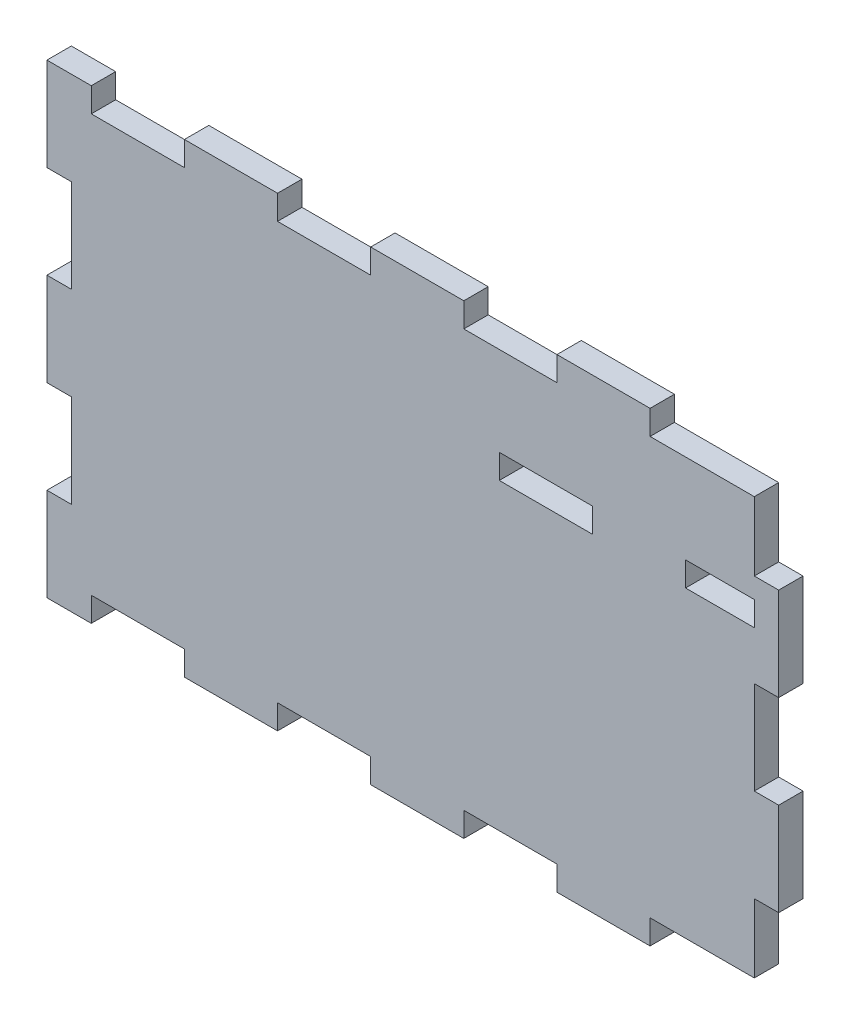
SolidWorks part; units mm, degrees
ref_plane "Alzado" through (0, 0, 0) normal (0, 0, 1) x (1, 0, 0)
ref_plane "Planta" through (0, 0, 0) normal (0, 1, 0) x (1, 0, 0)
ref_plane "Vista lateral" through (0, 0, 0) normal (1, 0, 0) x (0, 0, -1)
sketch "Croquis2" plane through (0, 0, 0) normal (0, 0, 1) x (1, 0, 0)
  line L11 (-60.2904, -48.8443) -> (-52.7904, -48.8443)
  line L12 (-52.7904, -48.8443) -> (-52.7904, -45.8443)
  line L13 (-52.7904, -45.8443) -> (-31.7904, -45.8443)
  line L14 (-31.7904, -45.8443) -> (-31.7904, -48.8443)
  line L15 (-31.7904, -48.8443) -> (-10.7904, -48.8443)
  line L16 (-10.7904, -48.8443) -> (-10.7904, -45.8443)
  line L17 (-10.7904, -45.8443) -> (10.2096, -45.8443)
  line L18 (10.2096, -45.8443) -> (10.2096, -48.8443)
  line L19 (10.2096, -48.8443) -> (31.2096, -48.8443)
  line L20 (31.2096, -48.8443) -> (31.2096, -45.8443)
  line L21 (31.2096, -45.8443) -> (52.2096, -45.8443)
  line L22 (52.2096, -45.8443) -> (52.2096, -48.8443)
  line L23 (52.2096, -48.8443) -> (73.2096, -48.8443)
  line L24 (73.2096, -48.8443) -> (73.2096, -45.8443)
  line L25 (73.2096, -45.8443) -> (94.2096, -45.8443)
  line L26 (94.2096, -45.8443) -> (96.7096, -45.8443)
  line L27 (96.7096, -45.8443) -> (96.7096, -30.3443)
  line L28 (96.7096, -30.3443) -> (99.7096, -30.3443)
  line L29 (99.7096, -30.3443) -> (99.7096, -9.3443)
  line L30 (99.7096, -9.3443) -> (96.7096, -9.3443)
  line L31 (96.7096, -9.3443) -> (96.7096, 11.6557)
  line L32 (96.7096, 11.6557) -> (99.7096, 11.6557)
  line L33 (99.7096, 11.6557) -> (99.7096, 32.6557)
  line L34 (99.7096, 32.6557) -> (96.7096, 32.6557)
  line L35 (96.7096, 32.6557) -> (96.7096, 48.1557)
  line L36 (96.7096, 48.1557) -> (73.2096, 48.1557)
  line L37 (73.2096, 48.1557) -> (73.2096, 51.1557)
  line L38 (73.2096, 51.1557) -> (52.2096, 51.1557)
  line L39 (52.2096, 51.1557) -> (52.2096, 48.1557)
  line L40 (52.2096, 48.1557) -> (31.2096, 48.1557)
  line L41 (31.2096, 48.1557) -> (31.2096, 51.1557)
  line L42 (31.2096, 51.1557) -> (10.2096, 51.1557)
  line L43 (10.2096, 51.1557) -> (10.2096, 48.1557)
  line L44 (10.2096, 48.1557) -> (-10.7904, 48.1557)
  line L45 (-10.7904, 48.1557) -> (-10.7904, 51.1557)
  line L46 (-10.7904, 51.1557) -> (-31.7904, 51.1557)
  line L47 (-31.7904, 51.1557) -> (-31.7904, 48.1557)
  line L48 (-31.7904, 48.1557) -> (-52.7904, 48.1557)
  line L49 (-52.7904, 48.1557) -> (-52.7904, 51.1557)
  line L50 (-52.7904, 51.1557) -> (-60.2904, 51.1557)
  line L54 (96.7096, 1.1557) -> (-60.2904, 1.1557) construction
  line L55 (-60.2904, 32.6557) -> (-57.2904, 32.6557)
  line L56 (60.2096, 28.0657) -> (39.2096, 28.0657)
  line L57 (96.7096, 28.0657) -> (81.2096, 28.0657)
  line L58 (96.7096, 28.0657) -> (96.7096, 22.5657)
  line L59 (96.7096, 22.5657) -> (81.2096, 22.5657)
  line L60 (81.2096, 28.0657) -> (81.2096, 22.5657)
  line L61 (60.2096, 28.0657) -> (60.2096, 22.5657)
  line L62 (60.2096, 22.5657) -> (39.2096, 22.5657)
  line L63 (39.2096, 28.0657) -> (39.2096, 22.5657)
  line L68 (-60.2904, -48.8443) -> (-60.2904, -30.3443)
  line L69 (-60.2904, 11.6557) -> (-57.2904, 11.6557)
  line L70 (-57.2904, 32.6557) -> (-57.2904, 11.6557)
  line L71 (-60.2904, 32.6557) -> (-60.2904, 51.1557)
  line L72 (-57.2904, -30.3443) -> (-57.2904, -9.3443)
  line L73 (-60.2904, -9.3443) -> (-57.2904, -9.3443)
  line L74 (-60.2904, -30.3443) -> (-57.2904, -30.3443)
  line L75 (-60.2904, -9.3443) -> (-60.2904, 11.6557)
  point P4 (-58.7904, 32.6557)
  point P11 (99.7096, 22.1557)
  dimension "D1" = 100
  dimension "D2" = 160
  dimension "D3" = 15.5
  dimension "D4" = 5.5
  dimension "D5" = 0
  dimension "D6" = 23.09
  dimension "D7" = 21
  dimension "D8" = 5.5
  dimension "D9" = 21
  dimension "D10" = 21
  dimension "D11" = 18.5
  dimension "D12" = 21
  dimension "D13" = 21
  dimension "D14" = 18.5
  dimension "D15" = 3
extrude "Saliente-Extruir1" add sketch "Croquis2" along normal blind 5.5
sketch "Croquis3" plane through (0, 51.1557, 0) normal (0, 1, 0) x (1, 0, 0)
  line L0 (73.2096, 0) -> (52.2096, 0) construction
  line L1 (52.2096, 0) -> (52.2096, -5.5) construction
  line L2 (52.2096, -5.5) -> (73.2096, -5.5) construction
  line L3 (73.2096, -5.5) -> (73.2096, 0) construction
  line L4 (31.2096, 0) -> (10.2096, 0) construction
  line L5 (10.2096, 0) -> (10.2096, -5.5) construction
  line L6 (10.2096, -5.5) -> (31.2096, -5.5) construction
  line L7 (31.2096, -5.5) -> (31.2096, 0) construction
  line L8 (-10.7904, 0) -> (-31.7904, 0) construction
  line L9 (-31.7904, 0) -> (-31.7904, -5.5) construction
  line L10 (-31.7904, -5.5) -> (-10.7904, -5.5) construction
  line L11 (-10.7904, -5.5) -> (-10.7904, 0) construction
  line L12 (-52.7904, 0) -> (-60.2904, 0) construction
  line L13 (-60.2904, 0) -> (-60.2904, -5.5) construction
  line L14 (-60.2904, -5.5) -> (-52.7904, -5.5) construction
  line L15 (-52.7904, -5.5) -> (-52.7904, 0) construction
  line L16 (73.2096, 0) -> (52.2096, 0)
  line L17 (52.2096, 0) -> (52.2096, -5.5)
  line L18 (52.2096, -5.5) -> (73.2096, -5.5)
  line L19 (73.2096, -5.5) -> (73.2096, 0)
  line L20 (31.2096, 0) -> (10.2096, 0)
  line L21 (10.2096, 0) -> (10.2096, -5.5)
  line L22 (10.2096, -5.5) -> (31.2096, -5.5)
  line L23 (31.2096, -5.5) -> (31.2096, 0)
  line L24 (-10.7904, 0) -> (-31.7904, 0)
  line L25 (-31.7904, 0) -> (-31.7904, -5.5)
  line L26 (-31.7904, -5.5) -> (-10.7904, -5.5)
  line L27 (-10.7904, -5.5) -> (-10.7904, 0)
  line L28 (-52.7904, 0) -> (-60.2904, 0)
  line L29 (-60.2904, 0) -> (-60.2904, -5.5)
  line L30 (-60.2904, -5.5) -> (-52.7904, -5.5)
  line L31 (-52.7904, -5.5) -> (-52.7904, 0)
extrude "Saliente-Extruir2" add sketch "Croquis3" along normal blind 2.5
sketch "Croquis4" plane through (-60.2904, 0, 0) normal (-1, 0, 0) x (0, 0, 1)
  line L0 (0, -30.3443) -> (0, -48.8443) construction
  line L1 (0, -48.8443) -> (5.5, -48.8443) construction
  line L2 (5.5, -48.8443) -> (5.5, -30.3443) construction
  line L3 (5.5, -30.3443) -> (0, -30.3443) construction
  line L4 (0, 11.6557) -> (0, -9.3443) construction
  line L5 (0, -9.3443) -> (5.5, -9.3443) construction
  line L6 (5.5, -9.3443) -> (5.5, 11.6557) construction
  line L7 (5.5, 11.6557) -> (0, 11.6557) construction
  line L8 (0, 53.6557) -> (0, 32.6557) construction
  line L9 (0, 32.6557) -> (5.5, 32.6557) construction
  line L10 (5.5, 32.6557) -> (5.5, 53.6557) construction
  line L11 (5.5, 53.6557) -> (0, 53.6557) construction
  line L12 (0, -30.3443) -> (0, -48.8443)
  line L13 (0, -48.8443) -> (5.5, -48.8443)
  line L14 (5.5, -48.8443) -> (5.5, -30.3443)
  line L15 (5.5, -30.3443) -> (0, -30.3443)
  line L16 (0, 11.6557) -> (0, -9.3443)
  line L17 (0, -9.3443) -> (5.5, -9.3443)
  line L18 (5.5, -9.3443) -> (5.5, 11.6557)
  line L19 (5.5, 11.6557) -> (0, 11.6557)
  line L20 (0, 53.6557) -> (0, 32.6557)
  line L21 (0, 32.6557) -> (5.5, 32.6557)
  line L22 (5.5, 32.6557) -> (5.5, 53.6557)
  line L23 (5.5, 53.6557) -> (0, 53.6557)
extrude "Saliente-Extruir3" add sketch "Croquis4" along normal blind 2.5
sketch "Croquis5" plane through (0, -48.8443, 0) normal (0, -1, 0) x (1, 0, 0)
  line L0 (-62.7904, 0) -> (-52.7904, 0) construction
  line L1 (-52.7904, 0) -> (-52.7904, 5.5) construction
  line L2 (-52.7904, 5.5) -> (-62.7904, 5.5) construction
  line L3 (-62.7904, 5.5) -> (-62.7904, 0) construction
  line L4 (-31.7904, 0) -> (-10.7904, 0) construction
  line L5 (-10.7904, 0) -> (-10.7904, 5.5) construction
  line L6 (-10.7904, 5.5) -> (-31.7904, 5.5) construction
  line L7 (-31.7904, 5.5) -> (-31.7904, 0) construction
  line L8 (10.2096, 0) -> (31.2096, 0) construction
  line L9 (31.2096, 0) -> (31.2096, 5.5) construction
  line L10 (31.2096, 5.5) -> (10.2096, 5.5) construction
  line L11 (10.2096, 5.5) -> (10.2096, 0) construction
  line L12 (52.2096, 0) -> (73.2096, 0) construction
  line L13 (73.2096, 0) -> (73.2096, 5.5) construction
  line L14 (73.2096, 5.5) -> (52.2096, 5.5) construction
  line L15 (52.2096, 5.5) -> (52.2096, 0) construction
  line L16 (-62.7904, 0) -> (-52.7904, 0)
  line L17 (-52.7904, 0) -> (-52.7904, 5.5)
  line L18 (-52.7904, 5.5) -> (-62.7904, 5.5)
  line L19 (-62.7904, 5.5) -> (-62.7904, 0)
  line L20 (-31.7904, 0) -> (-10.7904, 0)
  line L21 (-10.7904, 0) -> (-10.7904, 5.5)
  line L22 (-10.7904, 5.5) -> (-31.7904, 5.5)
  line L23 (-31.7904, 5.5) -> (-31.7904, 0)
  line L24 (10.2096, 0) -> (31.2096, 0)
  line L25 (31.2096, 0) -> (31.2096, 5.5)
  line L26 (31.2096, 5.5) -> (10.2096, 5.5)
  line L27 (10.2096, 5.5) -> (10.2096, 0)
  line L28 (52.2096, 0) -> (73.2096, 0)
  line L29 (73.2096, 0) -> (73.2096, 5.5)
  line L30 (73.2096, 5.5) -> (52.2096, 5.5)
  line L31 (52.2096, 5.5) -> (52.2096, 0)
extrude "Saliente-Extruir4" add sketch "Croquis5" along normal blind 2.5
sketch "Croquis6" plane through (99.7096, 0, 0) normal (1, 0, 0) x (0, 0, -1)
  line L0 (0, 11.6557) -> (0, 32.6557) construction
  line L1 (0, 32.6557) -> (-5.5, 32.6557) construction
  line L2 (-5.5, 32.6557) -> (-5.5, 11.6557) construction
  line L3 (-5.5, 11.6557) -> (0, 11.6557) construction
  line L4 (0, -30.3443) -> (0, -9.3443) construction
  line L5 (0, -9.3443) -> (-5.5, -9.3443) construction
  line L6 (-5.5, -9.3443) -> (-5.5, -30.3443) construction
  line L7 (-5.5, -30.3443) -> (0, -30.3443) construction
  line L8 (0, 11.6557) -> (0, 32.6557)
  line L9 (0, 32.6557) -> (-5.5, 32.6557)
  line L10 (-5.5, 32.6557) -> (-5.5, 11.6557)
  line L11 (-5.5, 11.6557) -> (0, 11.6557)
  line L12 (0, -30.3443) -> (0, -9.3443)
  line L13 (0, -9.3443) -> (-5.5, -9.3443)
  line L14 (-5.5, -9.3443) -> (-5.5, -30.3443)
  line L15 (-5.5, -30.3443) -> (0, -30.3443)
extrude "Saliente-Extruir5" add sketch "Croquis6" along normal blind 2.5
